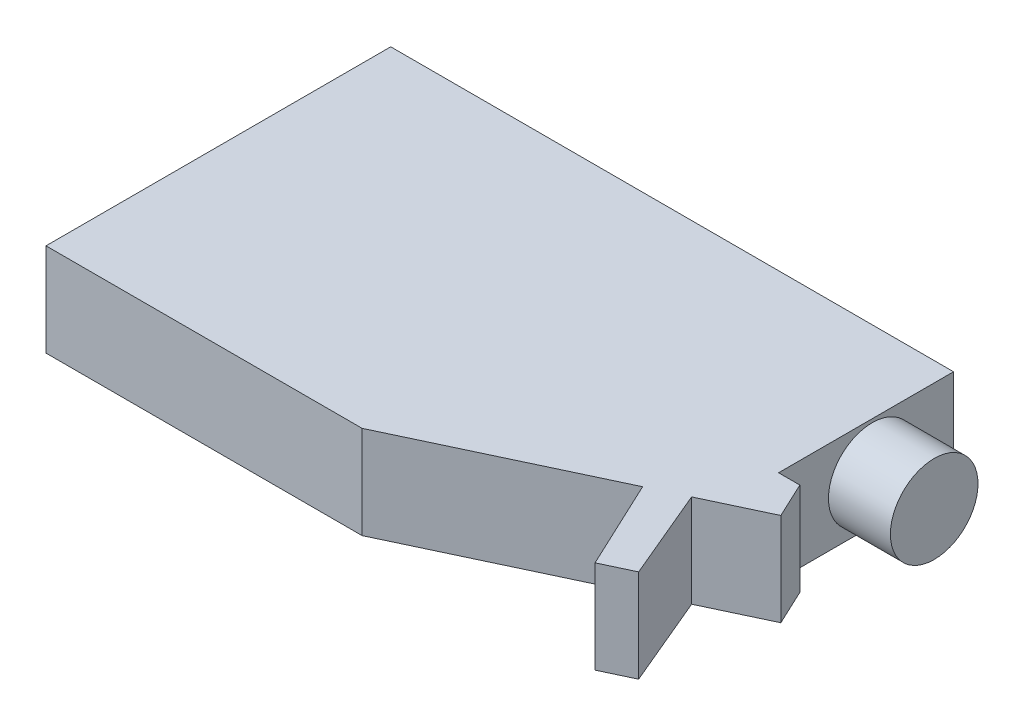
SolidWorks part; units mm, degrees
ref_plane "Front Plane" through (0, 0, 0) normal (0, 0, 1) x (1, 0, 0)
ref_plane "Top Plane" through (0, 0, 0) normal (0, 1, 0) x (1, 0, 0)
ref_plane "Right Plane" through (0, 0, 0) normal (1, 0, 0) x (0, 0, -1)
sketch "Sketch1" plane through (0, 0, 0) normal (0, 1, 0) x (1, 0, 0)
  line L0 (15.2455, -7.9489) -> (46.0498, 6.5291)
  line L1 (-35.7703, -7.9489) -> (15.2455, -7.9489)
  line L2 (-35.7703, -7.9489) -> (-35.7703, 47.6937)
  line L3 (-35.7703, 47.6937) -> (55.0749, 47.6937)
  line L5 (61.2278, 13.6628) -> (58.5081, 19.4495)
  line L6 (58.5081, 19.4495) -> (55.0749, 19.4495)
  line L7 (46.0498, 6.5291) -> (52.8544, -7.9489)
  line L8 (52.8544, -7.9489) -> (57.6399, -5.6998)
  line L9 (57.6399, -5.6998) -> (51.4299, 9.0577)
  line L11 (51.4299, 9.0577) -> (61.2278, 13.6628)
  line L12 (55.0749, 19.4495) -> (55.0749, 47.6937)
extrude "Boss-Extrude1" add sketch "Sketch1" along normal blind 15
sketch "Sketch2" plane through (55.0749, 0, 0) normal (1, 0, 0) x (0, 0, -1)
  circle A0 centre (34.5707, 7.3782) radius 7.0679
extrude "Boss-Extrude2" add sketch "Sketch2" along normal blind 10
